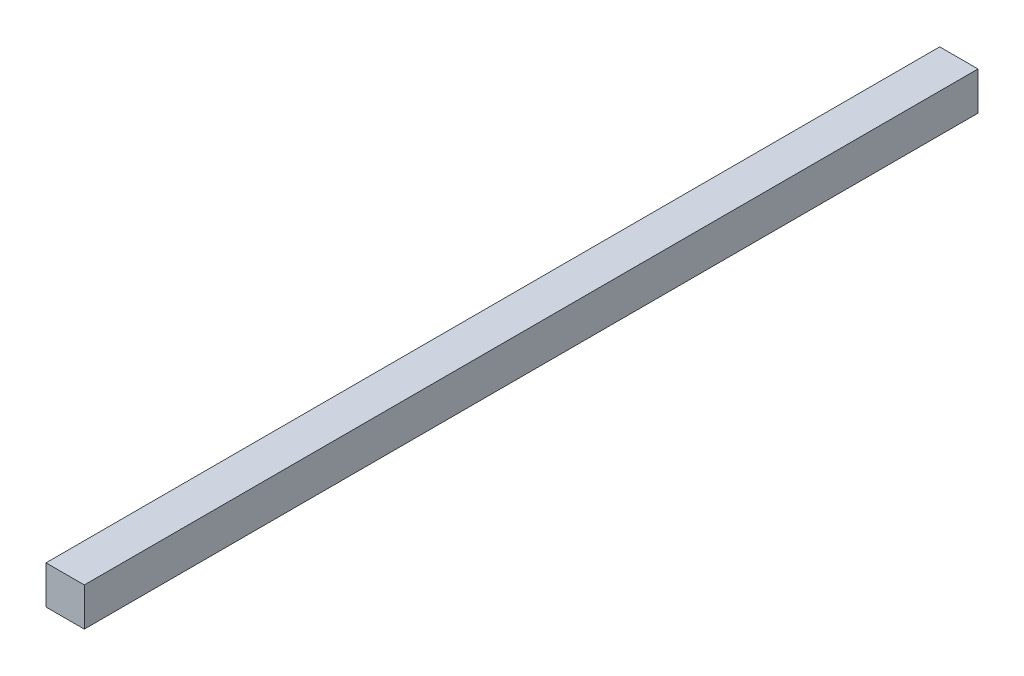
SolidWorks part; units mm, degrees
material "Beech"
ref_plane "Plan de face" through (0, 0, 0) normal (0, 0, 1) x (1, 0, 0)
ref_plane "Plan de dessus" through (0, 0, 0) normal (0, 1, 0) x (1, 0, 0)
ref_plane "Plan de droite" through (0, 0, 0) normal (1, 0, 0) x (0, 0, -1)
sketch "Sketch1" plane through (0, 0, 0) normal (0, 0, 1) x (1, 0, 0)
  line L1 (-7.5, -7.5) -> (7.5, -7.5)
  line L2 (-7.5, -7.5) -> (-7.5, 7.5)
  line L3 (-7.5, 7.5) -> (7.5, 7.5)
  line L4 (7.5, -7.5) -> (7.5, 7.5)
  line L5 (-7.5, -7.5) -> (7.5, 7.5) construction
  line L6 (-7.5, 7.5) -> (7.5, -7.5) construction
  point P0 (0, 0)
  dimension "D1" = 15
  dimension "D2" = 15
extrude "Boss-Extrude1" add sketch "Sketch1" along normal blind 350
